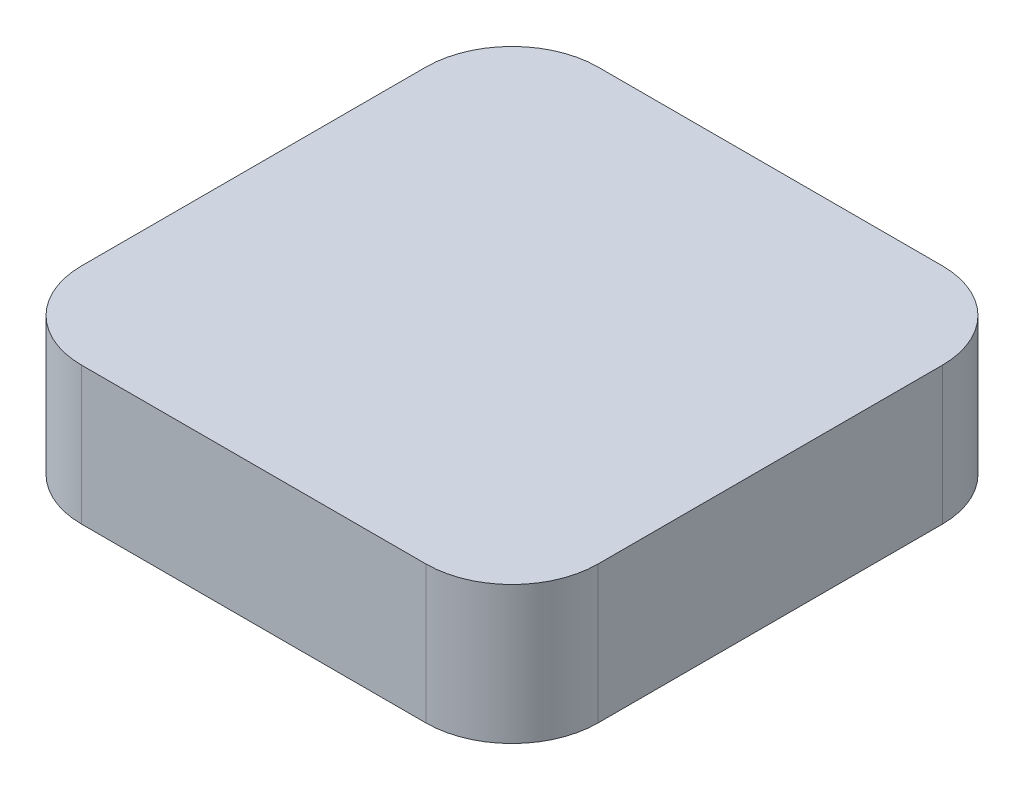
SolidWorks part; units mm, degrees
ref_plane "Front Plane" through (0, 0, 0) normal (0, 0, 1) x (1, 0, 0)
ref_plane "Top Plane" through (0, 0, 0) normal (0, 1, 0) x (1, 0, 0)
ref_plane "Right Plane" through (0, 0, 0) normal (1, 0, 0) x (0, 0, -1)
sketch "Sketch1" plane through (0, 0, 0) normal (0, 1, 0) x (1, 0, 0)
  line L1 (-5, 7.5) -> (5, 7.5)
  line L2 (-7.5, 5) -> (-7.5, -5)
  line L3 (-5, -7.5) -> (5, -7.5)
  line L4 (7.5, 5) -> (7.5, -5)
  arc A0 (7.5, -5) -> (5, -7.5) centre (5, -5) cw
  arc A1 (7.5, 5) -> (5, 7.5) centre (5, 5) ccw
  arc A2 (-5, 7.5) -> (-7.5, 5) centre (-5, 5) ccw
  arc A3 (-5, -7.5) -> (-7.5, -5) centre (-5, -5) cw
  point P0 (0, 0)
  point P8 (7.5, -7.5)
  point P11 (7.5, 7.5)
  point P16 (-7.5, -7.5)
  dimension "D3" = 2.5
  dimension "D1" = 15
  dimension "D2" = 15
extrude "Boss-Extrude1" add sketch "Sketch1" along normal blind 4
